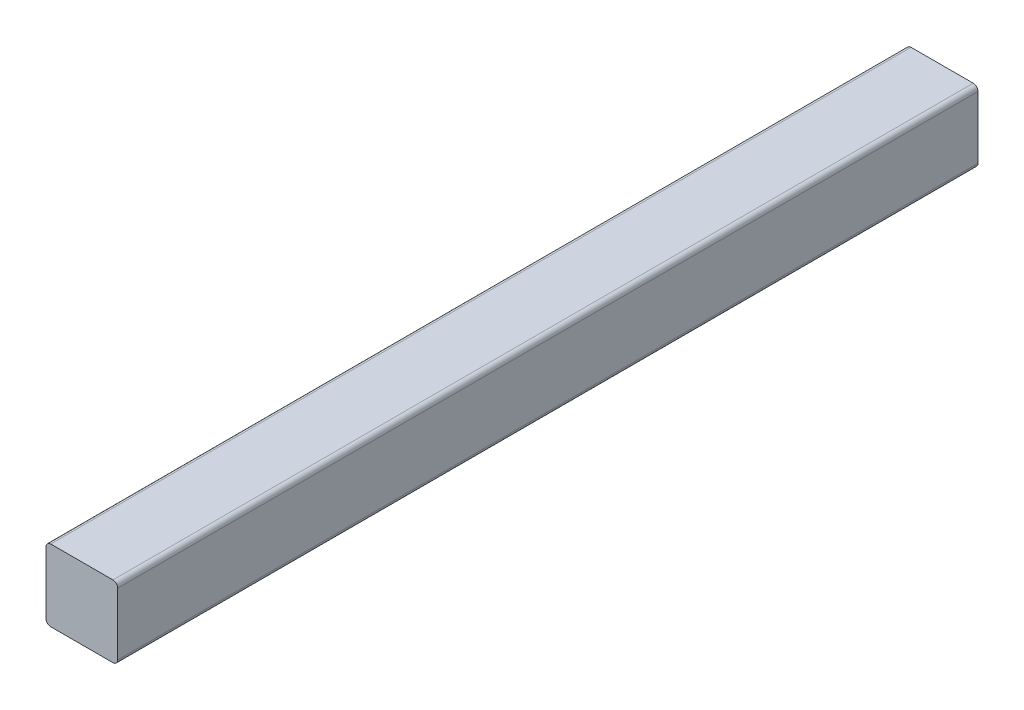
SolidWorks part; units mm, degrees
ref_plane "Front Plane" through (0, 0, 0) normal (0, 0, 1) x (1, 0, 0)
ref_plane "Top Plane" through (0, 0, 0) normal (0, 1, 0) x (1, 0, 0)
ref_plane "Right Plane" through (0, 0, 0) normal (1, 0, 0) x (0, 0, -1)
sketch "Sketch1" plane through (0, 0, 0) normal (0, 0, 1) x (1, 0, 0)
  line L0 (2, 0) -> (28, 0)
  line L1 (30, 2) -> (30, 28)
  line L2 (28, 30) -> (2, 30)
  line L3 (0, 28) -> (0, 2)
  arc A0 (2, 0) -> (0, 2) centre (2, 2) cw
  arc A1 (30, 2) -> (28, 0) centre (28, 2) cw
  arc A2 (28, 30) -> (30, 28) centre (28, 28) cw
  arc A3 (0, 28) -> (2, 30) centre (2, 28) cw
  point P7 (0, 0)
  dimension "D1" = 2
  dimension "D2" = 2
  dimension "D3" = 2
  dimension "D4" = 2
sketch "Sketch3" plane through (0, 0, 0) normal (0, 0, 1) x (1, 0, 0)
  line L0 (2, 0) -> (28, 0)
  line L1 (30, 2) -> (30, 28)
  line L2 (28, 30) -> (2, 30)
  line L3 (0, 28) -> (0, 2)
  arc A0 (2, 0) -> (0, 2) centre (2, 2) cw
  arc A1 (30, 2) -> (28, 0) centre (28, 2) cw
  arc A2 (28, 30) -> (30, 28) centre (28, 28) cw
  arc A3 (0, 28) -> (2, 30) centre (2, 28) cw
  dimension "D1" = 2
extrude "Boss-Extrude1" add sketch "Sketch3" along normal blind 360
